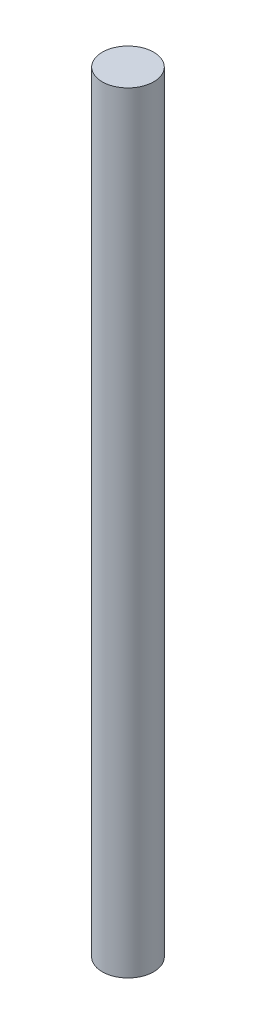
SolidWorks part; units mm, degrees
ref_plane "Front Plane" through (0, 0, 0) normal (0, 0, 1) x (1, 0, 0)
ref_plane "Top Plane" through (0, 0, 0) normal (0, 1, 0) x (1, 0, 0)
ref_plane "Right Plane" through (0, 0, 0) normal (1, 0, 0) x (0, 0, -1)
sketch "Sketch1" plane through (0, 0, 0) normal (0, 1, 0) x (1, 0, 0)
  circle A0 centre (0, 0) radius 5
  dimension "D1" = 10
extrude "Boss-Extrude1" add sketch "Sketch1" along normal blind 150
